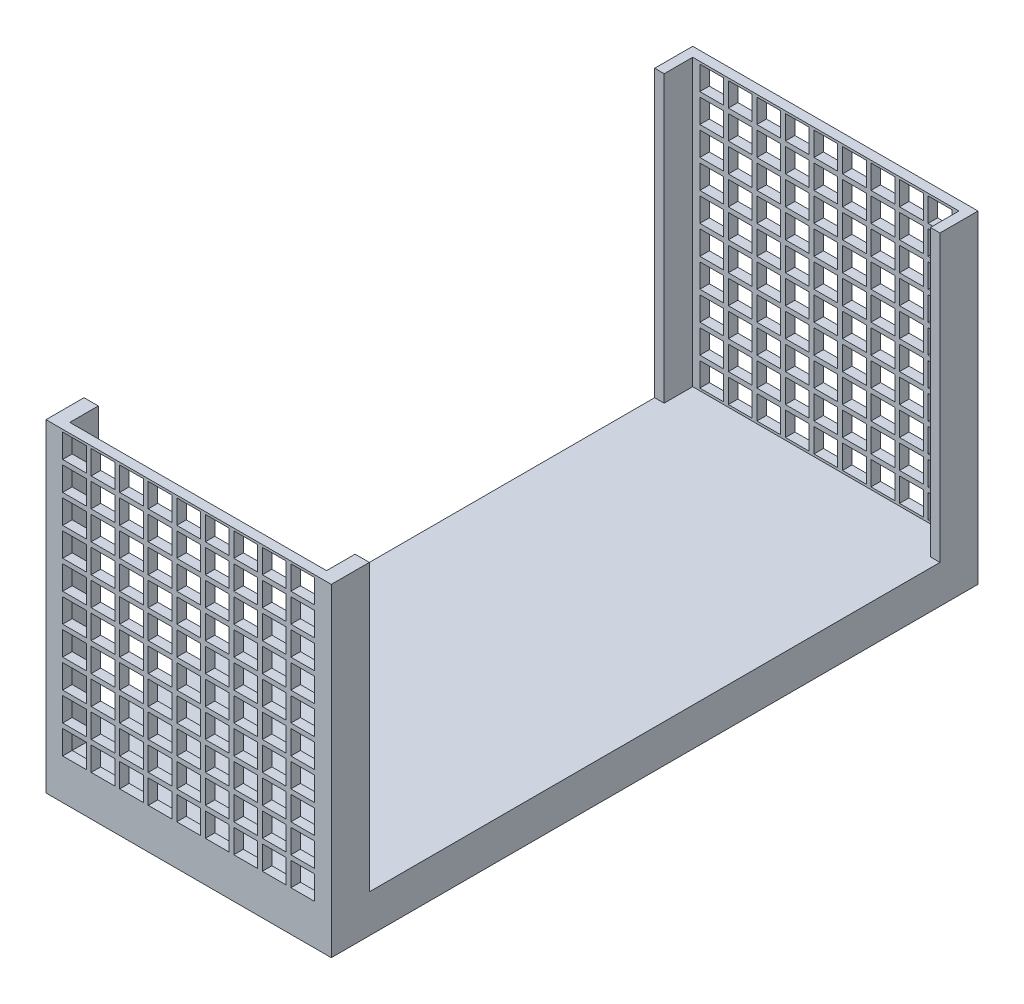
SolidWorks part; units mm, degrees
ref_plane "Front Plane" through (0, 0, 0) normal (0, 0, 1) x (1, 0, 0)
ref_plane "Top Plane" through (0, 0, 0) normal (0, 1, 0) x (1, 0, 0)
ref_plane "Right Plane" through (0, 0, 0) normal (1, 0, 0) x (0, 0, -1)
sketch "Sketch1" plane through (0, 0, 0) normal (0, 0, 1) x (1, 0, 0)
  line L1 (7.5, -8.5) -> (-7.5, -8.5)
  line L2 (7.5, -8.5) -> (7.5, 8.5)
  line L3 (7.5, 8.5) -> (-7.5, 8.5)
  line L4 (-7.5, -8.5) -> (-7.5, 8.5)
  line L5 (7.5, -8.5) -> (-7.5, 8.5) construction
  line L6 (7.5, 8.5) -> (-7.5, -8.5) construction
  point P0 (0, 0)
  dimension "D1" = 15
  dimension "D2" = 17
extrude "Boss-Extrude1" add sketch "Sketch1" along normal blind 34
sketch "Sketch2" plane through (7.5, 0, 0) normal (1, 0, 0) x (0, 0, -1)
  line L0 (-34, 8.5) -> (0, 8.5) construction
  line L1 (-32, 8.5) -> (-2, 8.5)
  line L2 (-32, 8.5) -> (-32, -6.5)
  line L3 (-32, -6.5) -> (-2, -6.5)
  line L4 (-2, 8.5) -> (-2, -6.5)
  line L5 (-34, -8.5) -> (-34, 8.5) construction
  line L6 (-34, -8.5) -> (0, -8.5) construction
  line L7 (0, -8.5) -> (0, 8.5) construction
  dimension "D1" = 2
  dimension "D2" = 2
  dimension "D3" = 2
extrude "Cut-Extrude1" cut sketch "Sketch2" against normal up to next
sketch "Sketch5" plane through (0, 0, 0) normal (0, 0, -1) x (-1, 0, 0)
  line L0 (-7.5, 8.5) -> (7.5, 8.5) construction
  line L1 (-7, 8.5) -> (7, 8.5)
  line L2 (-7, 8.5) -> (-7, -6.5)
  line L3 (-7, -6.5) -> (7, -6.5)
  line L4 (7, 8.5) -> (7, -6.5)
  line L5 (-7, 8.5) -> (-7.5, 8.5) construction
  line L6 (-7.5, 8.5) -> (7, 8.5) construction
  line L7 (-7.5, -8.5) -> (-7.5, 8.5) construction
  line L8 (7, 8.5) -> (7.5, 8.5) construction
  line L9 (7.5, -8.5) -> (-7.5, -8.5) construction
  dimension "D1" = 0.5
  dimension "D2" = 2
extrude "Cut-Extrude4" cut sketch "Sketch5" along normal blind 1.5 from surface at -2 starting at face at (0, 1, 2)
sketch "Sketch3" plane through (0, 0, 34) normal (0, 0, 1) x (1, 0, 0)
  line L0 (7.5, 8.5) -> (-7.5, 8.5) construction
  line L1 (-6.75, 8.5) -> (6.75, 8.5)
  line L2 (-6.75, 8.5) -> (-6.75, -6.5)
  line L3 (-6.75, -6.5) -> (6.75, -6.5)
  line L4 (6.75, 8.5) -> (6.75, -6.5)
  line L5 (-7.5, 8.5) -> (-7.5, -8.5) construction
  line L7 (-7.5, -8.5) -> (7.5, -8.5) construction
  line L8 (7.5, 8.5) -> (6.75, 8.5) construction
  line L9 (-6.75, 8.5) -> (-7.5, 8.5) construction
  dimension "D1" = 0.75
  dimension "D3" = 2
extrude "Cut-Extrude2" cut sketch "Sketch3" along normal blind 1.5 from surface at -2 starting at face at (0, 1, 32)
sketch "Sketch6" plane through (0, 0, 33.5) normal (0, 0, -1) x (-1, 0, 0)
  line L0 (-6.625, 8.375) -> (-6.625, 8.5) construction
  line L1 (-5.375, 7.125) -> (-6.625, 7.125)
  line L2 (-5.375, 7.125) -> (-5.375, 8.375)
  line L3 (-5.375, 8.375) -> (-6.625, 8.375)
  line L4 (-6.625, 7.125) -> (-6.625, 8.375)
  line L5 (-5.375, 7.125) -> (-6.625, 8.375) construction
  line L6 (-5.375, 8.375) -> (-6.625, 7.125) construction
  line L7 (-6.75, 8.5) -> (6.75, 8.5) construction
  line L8 (-6.625, 8.375) -> (-6.75, 8.375) construction
  line L9 (-6.75, -6.5) -> (-6.75, 8.5) construction
  point P0 (-6, 7.75)
  dimension "D1" = 1.25
  dimension "D2" = 0.125
extrude "Cut-Extrude5" cut sketch "Sketch6" along normal through all from surface at -0.5 starting at face at (0, 0, 34)
pattern_linear "LPattern1" count 9 spacing 1.5 along (-1, 0, 0) count 10 spacing 1.5 along (0, -1, 0) of "Cut-Extrude5"
